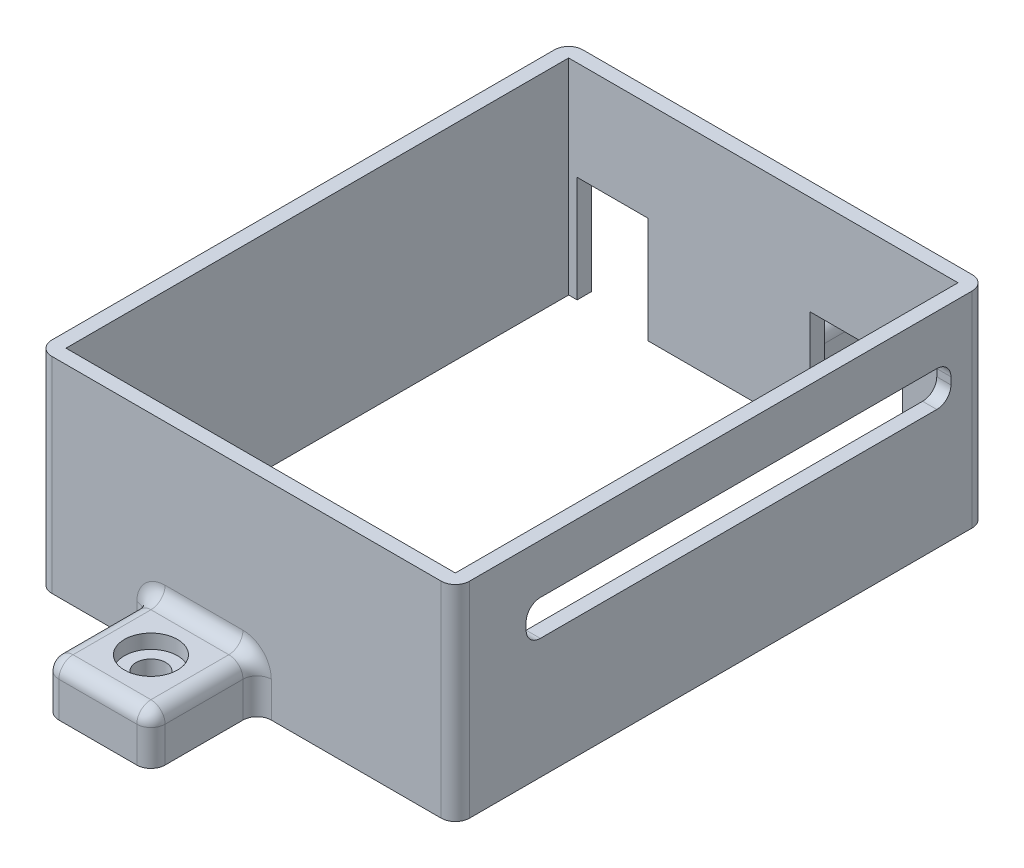
SolidWorks part; units mm, degrees
ref_plane "Front Plane" through (0, 0, 0) normal (0, 0, 1) x (1, 0, 0)
ref_plane "Top Plane" through (0, 0, 0) normal (0, 1, 0) x (1, 0, 0)
ref_plane "Right Plane" through (0, 0, 0) normal (1, 0, 0) x (0, 0, -1)
sketch "Sketch1" plane through (0, 0, 0) normal (0, 1, 0) x (1, 0, 0)
  line L0 (0, 0) -> (70.6232, 0) construction
  line L1 (-27.5, 35.5) -> (27.5, 35.5)
  line L2 (-27.5, 35.5) -> (-27.5, -35.5)
  line L3 (-27.5, -35.5) -> (27.5, -35.5)
  line L4 (27.5, 35.5) -> (27.5, -35.5)
  line L5 (0, 0) -> (0, -50.4544) construction
  line L6 (-27.5, 37.5) -> (27.5, 37.5)
  line L7 (29.5, 35.5) -> (29.5, -35.5)
  line L8 (-27.5, -37.5) -> (27.5, -37.5)
  line L9 (-29.5, 35.5) -> (-29.5, -35.5)
  line L10 (29.5, 37.5) -> (29.5, -37.5) construction
  line L11 (-29.5, -37.5) -> (29.5, -37.5) construction
  line L12 (-29.5, 37.5) -> (-29.5, -37.5) construction
  line L13 (-29.5, 37.5) -> (29.5, 37.5) construction
  arc A0 (29.5, -35.5) -> (27.5, -37.5) centre (27.5, -35.5) cw
  arc A1 (-27.5, -37.5) -> (-29.5, -35.5) centre (-27.5, -35.5) cw
  arc A2 (27.5, 37.5) -> (29.5, 35.5) centre (27.5, 35.5) cw
  arc A3 (-27.5, 37.5) -> (-29.5, 35.5) centre (-27.5, 35.5) ccw
  dimension "D4" = 2
  dimension "D5" = 2
  dimension "D6" = 2
  dimension "D7" = 2
  dimension "D1" = 55
  dimension "D2" = 71
  dimension "D3" = 2
extrude "Boss-Extrude1" add sketch "Sketch1" along normal blind 29 contours L2 L3 L4 L1
sketch "Sketch2" plane through (0, 0, -37.5) normal (0, 0, -1) x (-1, 0, 0)
  line L0 (-27.5, 0) -> (27.5, 0) construction
  line L1 (-19.6256, 0) -> (-6.6256, 0)
  line L2 (-19.6256, 0) -> (-19.6256, 15)
  line L3 (-19.6256, 15) -> (-6.6256, 15)
  line L4 (-6.6256, 0) -> (-6.6256, 15)
  line L5 (-29.5, 29) -> (-29.5, 0) construction
  line L6 (29.5, 29) -> (29.5, 0) construction
  line L7 (16.3, 0) -> (26.3, 0)
  line L8 (16.3, 0) -> (16.3, 15)
  line L9 (16.3, 15) -> (26.3, 15)
  line L10 (26.3, 0) -> (26.3, 15)
  dimension "D1" = 13
  dimension "D2" = 22.8744
  dimension "D3" = 15
  dimension "D5" = 10
  dimension "D8" = 3.2
extrude "Cut-Extrude1" cut sketch "Sketch2" against normal blind 27
sketch "Sketch3" plane through (29.5, 0, 0) normal (1, 0, 0) x (0, 0, -1)
  line L0 (-35.5, 29) -> (35.5, 29) construction
  line L1 (-25.5, 22) -> (30.5, 22)
  line L2 (-27.5, 20) -> (-27.5, 19)
  line L3 (-25.5, 17) -> (30.5, 17)
  line L4 (32.5, 20) -> (32.5, 19)
  line L5 (-37.5, 29) -> (-37.5, 0) construction
  arc A0 (30.5, 22) -> (32.5, 20) centre (30.5, 20) cw
  arc A1 (30.5, 17) -> (32.5, 19) centre (30.5, 19) ccw
  arc A2 (-27.5, 19) -> (-25.5, 17) centre (-25.5, 19) ccw
  arc A3 (-25.5, 22) -> (-27.5, 20) centre (-25.5, 20) ccw
  dimension "D4" = 2
  dimension "D5" = 2
  dimension "D6" = 2
  dimension "D7" = 2
  dimension "D1" = 5
  dimension "D2" = 7
  dimension "D3" = 60
  dimension "D8" = 10
extrude "Cut-Extrude2" cut sketch "Sketch3" against normal blind 27
sketch "Sketch4" plane through (0, 0, 0) normal (0, -1, 0) x (1, 0, 0)
  line L0 (-27.5, 37.5) -> (27.5, 37.5) construction
  line L1 (-13.5, 37.5) -> (1.5, 37.5)
  line L2 (-13.5, 37.5) -> (-13.5, 52.5)
  line L3 (-13.5, 52.5) -> (1.5, 52.5)
  line L4 (1.5, 37.5) -> (1.5, 52.5)
  line L5 (-6, 0) -> (-6, 66.8615) construction
  dimension "D1" = 15
  dimension "D2" = 15
  dimension "D3" = 6
extrude "Boss-Extrude2" add sketch "Sketch4" against normal blind 7
fillet "Fillet1" radius 2 5 edges at (1.5, 7, 45) (-6, 7, 52.5) (-13.5, 7, 45) (-13.5, 3.5, 52.5) (1.5, 3.5, 52.5)
sketch "Sketch5" plane through (0, 7, 0) normal (0, 1, 0) x (1, 0, 0)
  line L0 (-6, -30.1278) -> (-6, -51.0844) construction
  line L1 (1.5, -37.5) -> (1.5, -50.5) construction
  line L2 (-13.5, -50.5) -> (-13.5, -37.5) construction
  line L3 (-12.7676, -45) -> (14.974, -45) construction
  line L4 (-27.5, -37.5) -> (27.5, -37.5) construction
  line L5 (-0.5, -52.5) -> (-11.5, -52.5) construction
  circle A0 centre (-6, -45) radius 2.1
  dimension "D1" = 4.2
extrude "Cut-Extrude3" cut sketch "Sketch5" against normal blind 15
sketch "Sketch6" plane through (0, 7, 0) normal (0, 1, 0) x (1, 0, 0)
  circle A0 centre (-6, -45) radius 3.75
  circle A1 centre (-6, -45) radius 2.1 construction
  dimension "D1" = 7.5
extrude "Cut-Extrude4" cut sketch "Sketch6" against normal blind 2 contours A0
mirror "Mirror2" about plane through (0, 0, 0) normal (0, 0, 1) of "Fillet1", "Boss-Extrude2", "Cut-Extrude4", "Cut-Extrude3"
fillet "Fillet2" radius 2 10 edges at (-13.5, 2.5, 37.5) (-12.9142, 6.4142, 37.5) (1.5, 2.5, 37.5) (0.9142, 6.4142, 37.5) (-13.5, 2.5, -37.5) (-12.9142, 6.4142, -37.5) (1.5, 2.5, -37.5) (0.9142, 6.4142, -37.5) (-6, 7, 37.5) (-6, 7, -37.5)
